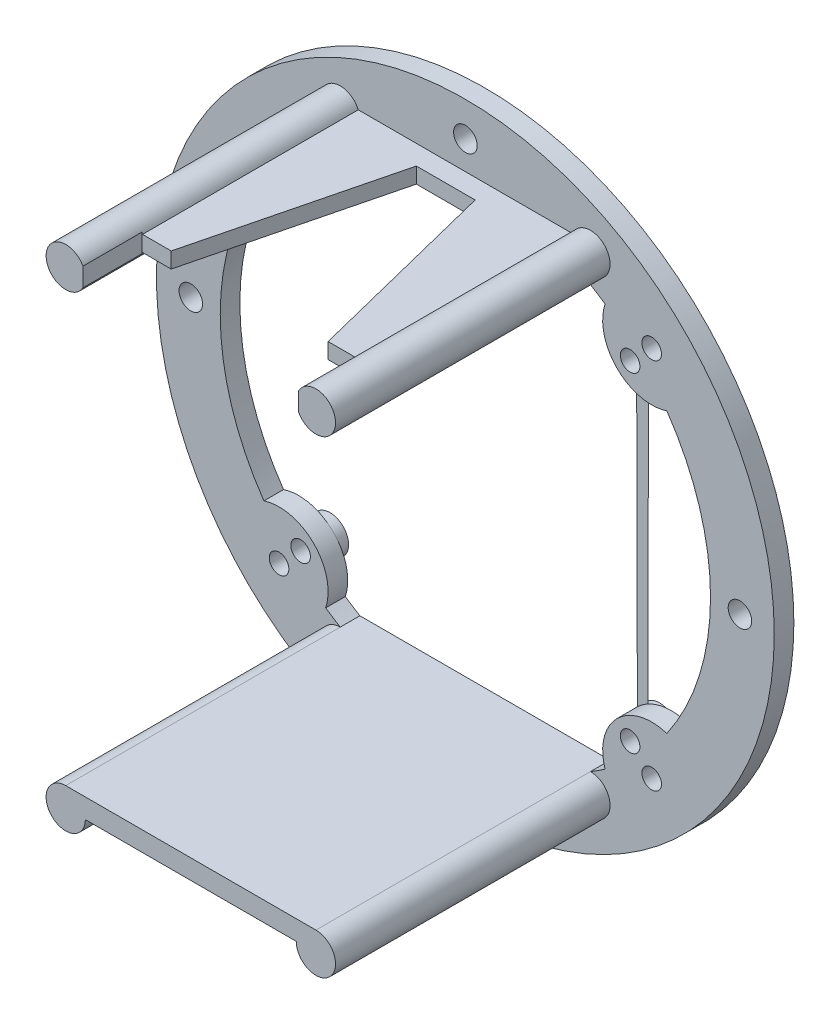
SolidWorks part; units mm, degrees
ref_plane "Front Plane" through (0, 0, 0) normal (0, 0, 1) x (1, 0, 0)
ref_plane "Top Plane" through (0, 0, 0) normal (0, 1, 0) x (1, 0, 0)
ref_plane "Right Plane" through (0, 0, 0) normal (1, 0, 0) x (0, 0, -1)
sketch "Sketch1" plane through (0, 0, 0) normal (0, 0, 1) x (1, 0, 0)
  line L0 (-12.7574, -21.5) -> (12.7574, -21.5)
  line L1 (-8.5294, 23.5) -> (8.5294, 23.5)
  line L2 (-34.8306, 0) -> (34.9783, 0) construction
  line L3 (0, 32.4678) -> (0, -35.8331) construction
  circle A0 centre (0, 0) radius 31.5
  arc A1 (-8.5294, 23.5) -> (-14.2446, 20.5448) centre (0, 0) ccw
  arc A2 (12.7574, -21.5) -> (14.2446, -20.5448) centre (0, 0) ccw
  arc A3 (-20.5448, 14.2446) -> (-14.2446, 20.5448) centre (-19, 19) ccw
  arc A5 (-14.2446, -20.5448) -> (-20.5448, -14.2446) centre (-19, -19) ccw
  arc A7 (-20.5448, 14.2446) -> (-20.5448, -14.2446) centre (0, 0) ccw
  arc A8 (14.2446, 20.5448) -> (8.5294, 23.5) centre (0, 0) ccw
  arc A9 (14.2446, 20.5448) -> (20.5448, 14.2446) centre (19, 19) ccw
  arc A10 (20.5448, -14.2446) -> (20.5448, 14.2446) centre (0, 0) ccw
  arc A11 (20.5448, -14.2446) -> (14.2446, -20.5448) centre (19, -19) ccw
  arc A12 (-14.2446, -20.5448) -> (-12.7574, -21.5) centre (0, 0) ccw
  point P10 (0, -25)
  point P11 (0, 25)
  point P19 (0, 0)
  point P21 (0, 31.5)
  point P24 (0, -31.5)
  dimension "D1" = 50
  dimension "D2" = 63
  dimension "D3" = 8
  dimension "D7" = 5
  dimension "D4" = 10
  dimension "D5" = 38
  dimension "D6" = 38
extrude "Boss-Extrude1" add sketch "Sketch1" along normal blind 2
sketch "Sketch2" plane through (0, 0, 0) normal (0, 0, 1) x (1, 0, 0)
  line L0 (-16.8, 16.8) -> (-16.8, -16.8) construction
  line L1 (-16.8, -16.8) -> (16.8, -16.8) construction
  line L2 (16.8, -16.8) -> (16.8, 16.8) construction
  line L3 (16.8, 16.8) -> (-16.8, 16.8) construction
  line L4 (16.8, 16.8) -> (-16.8, -16.8) construction
  circle A0 centre (-19, 19) radius 1
  circle A1 centre (-16.8, 16.8) radius 1
  circle A2 centre (19, 19) radius 1
  circle A3 centre (16.8, 16.8) radius 1
  circle A4 centre (-19, -19) radius 1
  circle A5 centre (-16.8, -16.8) radius 1
  circle A6 centre (19, -19) radius 1
  circle A7 centre (16.8, -16.8) radius 1
  circle A9 centre (-28, 0) radius 1.2
  circle A10 centre (28, 0) radius 1.2
  circle A11 centre (0, 28) radius 1.2
  circle A12 centre (0, -28) radius 1.2
  circle A13 centre (0, 0) radius 28 construction
  point P29 (0, 0)
  point P30 (0, 0)
  point P31 (0, 0)
  dimension "D1" = 2
  dimension "D3" = 2.4
  dimension "D4" = 56
  dimension "D2" = 33.6
extrude "Cut-Extrude2" cut sketch "Sketch2" along normal through all
sketch "Sketch5" plane through (0, 0, 0) normal (0, 0, -1) x (-1, 0, 0)
  line L0 (-19, 19) -> (-16.8, 16.8) construction
  line L1 (-17.6645, 20.3355) -> (-15.4645, 18.1355)
  line L2 (-20.3355, 17.6645) -> (-18.1355, 15.4645)
  line L3 (19, 19) -> (16.8, 16.8) construction
  line L4 (20.3355, 17.6645) -> (18.1355, 15.4645)
  line L5 (17.6645, 20.3355) -> (15.4645, 18.1355)
  line L6 (19, -19) -> (16.8, -16.8) construction
  line L7 (17.6645, -20.3355) -> (15.4645, -18.1355)
  line L8 (20.3355, -17.6645) -> (18.1355, -15.4645)
  line L9 (-19, -19) -> (-16.8, -16.8) construction
  line L10 (-20.3355, -17.6645) -> (-18.1355, -15.4645)
  line L11 (-17.6645, -20.3355) -> (-15.4645, -18.1355)
  arc A0 (-17.6645, 20.3355) -> (-20.3355, 17.6645) centre (-19, 19) ccw
  arc A1 (-18.1355, 15.4645) -> (-15.4645, 18.1355) centre (-16.8, 16.8) ccw
  arc A2 (-20.5448, 14.2446) -> (-14.2446, 20.5448) centre (-19, 19) ccw construction
  arc A3 (20.3355, 17.6645) -> (17.6645, 20.3355) centre (19, 19) ccw
  arc A4 (15.4645, 18.1355) -> (18.1355, 15.4645) centre (16.8, 16.8) ccw
  arc A5 (17.6645, -20.3355) -> (20.3355, -17.6645) centre (19, -19) ccw
  arc A6 (18.1355, -15.4645) -> (15.4645, -18.1355) centre (16.8, -16.8) ccw
  arc A7 (-20.3355, -17.6645) -> (-17.6645, -20.3355) centre (-19, -19) ccw
  arc A8 (-15.4645, -18.1355) -> (-18.1355, -15.4645) centre (-16.8, -16.8) ccw
  circle A9 centre (-19, 19) radius 1
  circle A10 centre (-16.8, 16.8) radius 1
  circle A11 centre (16.8, 16.8) radius 1
  circle A12 centre (19, 19) radius 1
  circle A13 centre (16.8, -16.8) radius 1
  circle A14 centre (19, -19) radius 1
  circle A15 centre (-16.8, -16.8) radius 1
  circle A16 centre (-19, -19) radius 1
  point P4 (-17.9, 17.9)
  point P17 (17.9, 17.9)
  point P24 (17.9, -17.9)
  point P31 (-17.9, -17.9)
  dimension "D1" = 4
  dimension "D2" = 4
extrude "Boss-Extrude3" add sketch "Sketch5" along normal blind 1
sketch "Sketch3" plane through (0, 0, 0) normal (0, 0, 1) x (1, 0, 0)
  line L0 (-8.5294, 0) -> (10.7574, 0) construction
  line L1 (-10.9243, 23.5) -> (10.9243, 23.5)
  line L3 (-10.9243, 25.1) -> (10.9243, 25.1)
  line L5 (-12.7574, -21.5) -> (12.7574, -21.5)
  line L7 (-10.7574, -23.5) -> (10.7574, -23.5)
  line L9 (-12.7574, -21.5) -> (12.7574, -21.5) construction
  line L10 (8.5294, 23.5) -> (-8.5294, 23.5) construction
  arc A1 (10.7574, -23.5) -> (12.7574, -21.5) centre (12.7574, -23.5) ccw
  arc A2 (-12.7574, -21.5) -> (-10.7574, -23.5) centre (-12.7574, -23.5) ccw
  arc A3 (-10.9243, 25.1) -> (-10.9243, 23.5) centre (-12.7574, 24.3) ccw
  arc A4 (10.9243, 23.5) -> (10.9243, 25.1) centre (12.7574, 24.3) ccw
  point P12 (0, 0)
  point P14 (-8.5294, 23.5)
  point P15 (0, 0)
  point P19 (0, 0)
  point P26 (-10.7867, 23.8415)
  point P29 (-11.5574, 25.1)
  point P30 (11.5413, 25.0879)
  point P31 (0, 0)
  point P32 (12.7574, 24.5509)
  point P33 (0, 0)
  dimension "D3" = 4
  dimension "D1" = 1.6
  dimension "D2" = 2
  dimension "D4" = 0.8
extrude "Boss-Extrude2" add sketch "Sketch3" along normal blind 30
sketch "Sketch4" plane through (0, 0, 0) normal (0, 1, 0) x (1, 0, 0)
  line L0 (-11, -30) -> (-11, -24)
  line L2 (-8, -24) -> (-3, -4)
  line L3 (-3, -4) -> (3, -4)
  line L4 (3, -4) -> (8, -24)
  line L6 (11, -24) -> (11, -30)
  line L7 (11, -30) -> (-11, -30)
  line L8 (0, 0) -> (0, -21.7594) construction
  line L9 (-8, -24) -> (-11, -24)
  line L10 (8, -24) -> (11, -24)
  line L11 (10.9243, -30) -> (-10.9243, -30) construction
  dimension "D1" = 4
  dimension "D2" = 6
  dimension "D3" = 22
  dimension "D4" = 6
  dimension "D5" = 16
extrude "Cut-Extrude3" cut sketch "Sketch4" along normal through all
